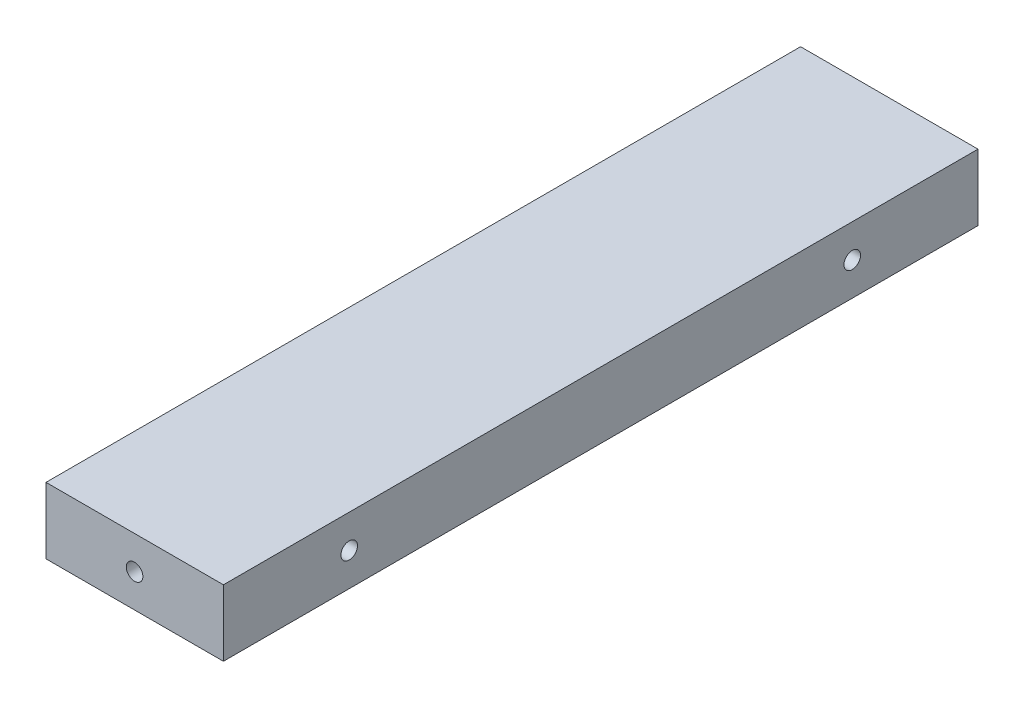
SolidWorks part; units mm, degrees
material "Beech"
ref_plane "Front Plane" through (0, 0, 0) normal (0, 0, 1) x (1, 0, 0)
ref_plane "Top Plane" through (0, 0, 0) normal (0, 1, 0) x (1, 0, 0)
ref_plane "Right Plane" through (0, 0, 0) normal (1, 0, 0) x (0, 0, -1)
sketch "Sketch1" plane through (0, 0, 0) normal (0, 0, 1) x (1, 0, 0)
  line L0 (-6.0809, -132.7) -> (-6.0809, 132.7) construction
  line L1 (-40.0809, -120) -> (-6.0809, -120)
  line L2 (-40.0809, -120) -> (-40.0809, -132.7)
  line L3 (-40.0809, -132.7) -> (-6.0809, -132.7)
  line L4 (-6.0809, -120) -> (-6.0809, -132.7)
  dimension "D1" = 12.7
extrude "Boss-Extrude1" add sketch "Sketch1" along normal up to surface (144.6 mm away)
hole_wizard "Hole1" positions "Sketch2" profile "Sketch3" legacy
sketch "Sketch2" plane through (12.9191, 0, 155.0243) normal (1, 0, 0) x (0, -1, 0)
  line L21 (0, 109.0243) -> (0, 155.0243) construction
  point P37 (126.35, 161.3743)
  point P42 (146.0833, 4.0743)
  point P44 (172.1667, 4.0743)
  point P63 (126.35, 34.5243)
  point P65 (126.35, 130.9243)
  point P76 (-172.1667, 4.0743)
  point P77 (-146.0833, 4.0743)
  point P78 (-126.35, 34.5243)
  point P79 (-126.35, 130.9243)
  point P80 (-126.35, 161.3743)
sketch "Sketch3" plane through (12.9191, -126.35, -6.35) normal (0, 1, 0) x (0, 0, -1)
  line L0 (0, 0) -> (0, 32.7039)
  line L1 (0, 32.7039) -> (1.5875, 31.75)
  line L2 (1.5875, 31.75) -> (1.5875, 4.0177)
  line L3 (1.5875, 4.0177) -> (5.08, 0)
  line L4 (5.08, 0) -> (0, 0)
  line L5 (0, -14.3089) -> (0, 102.4216) construction
  line L6 (0, 32.7039) -> (-1.5875, 31.75) construction
  line L7 (-1.5875, 4.0177) -> (-5.08, 0) construction
  dimension "Diameter" = 3.175
  dimension "Depth" = 31.75
  dimension "C-Sink Diameter" = 10.16
  dimension "C-Sink Angle" = 82
  dimension "Drill Angle" = 118
hole_wizard "Hole2" positions "Sketch4" profile "Sketch5" legacy
sketch "Sketch4" plane through (12.9191, 0, -10.4243) normal (1, 0, 0) x (0, 1, 0)
  line L21 (0, 109.0243) -> (0, 155.0243) construction
  point P37 (126.35, 161.3743)
  point P42 (146.0833, 4.0743)
  point P44 (172.1667, 4.0743)
  point P63 (126.35, 34.5243)
  point P65 (126.35, 130.9243)
  point P76 (-172.1667, 4.0743)
  point P77 (-146.0833, 4.0743)
  point P78 (-126.35, 34.5243)
  point P79 (-126.35, 130.9243)
  point P80 (-126.35, 161.3743)
sketch "Sketch5" plane through (12.9191, 126.35, 150.95) normal (0, 1, 0) x (0, 0, -1)
  line L0 (0, 0) -> (0, 32.7039)
  line L1 (0, 32.7039) -> (1.5875, 31.75)
  line L2 (1.5875, 31.75) -> (1.5875, 4.0177)
  line L3 (1.5875, 4.0177) -> (5.08, 0)
  line L4 (5.08, 0) -> (0, 0)
  line L5 (0, -14.3089) -> (0, 102.4216) construction
  line L6 (0, 32.7039) -> (-1.5875, 31.75) construction
  line L7 (-1.5875, 4.0177) -> (-5.08, 0) construction
  dimension "Diameter" = 3.175
  dimension "Depth" = 31.75
  dimension "C-Sink Diameter" = 10.16
  dimension "C-Sink Angle" = 82
  dimension "Drill Angle" = 118
hole_wizard "Hole5" positions "Sketch8" profile "Sketch9" legacy
sketch "Sketch8" plane through (-195.3677, 0, 157.3) normal (0, 0, 1) x (0, -1, 0)
  line L0 (120, 172.2617) -> (217.3, 172.2617) construction
  point P8 (126.35, 172.2617)
  point P10 (207.775, 172.2617)
sketch "Sketch9" plane through (-23.1059, -207.775, 157.3) normal (1, 0, 0) x (0, -1, 0)
  line L0 (0, 0) -> (0, 32.7039)
  line L1 (0, 32.7039) -> (1.5875, 31.75)
  line L2 (1.5875, 31.75) -> (1.5875, 4.0177)
  line L3 (1.5875, 4.0177) -> (5.08, 0)
  line L4 (5.08, 0) -> (0, 0)
  line L5 (0, -14.3089) -> (0, 102.4216) construction
  line L6 (0, 32.7039) -> (-1.5875, 31.75) construction
  line L7 (-1.5875, 4.0177) -> (-5.08, 0) construction
  dimension "Diameter" = 3.175
  dimension "Depth" = 31.75
  dimension "C-Sink Diameter" = 10.16
  dimension "C-Sink Angle" = 82
  dimension "Drill Angle" = 118
hole_wizard "Hole6" positions "Sketch10" profile "Sketch11" legacy
sketch "Sketch10" plane through (-52.7809, 0, -10.4243) normal (-1, 0, 0) x (0, -1, 0)
  line L12 (0, 0) -> (0, 155.0243) construction
  point P0 (-207.775, 333.0214)
  point P3 (-207.775, 225.489)
  point P6 (-207.775, 137.4243)
  point P9 (-172.1667, 4.0743)
  point P12 (-146.0833, 4.0743)
  point P15 (-94.6, 161.3743)
  point P18 (0, 161.3743)
  point P21 (94.6, 161.3743)
  point P24 (146.0833, 4.0743)
  point P27 (172.1667, 4.0743)
  point P30 (207.775, 137.4243)
  point P33 (207.775, 225.489)
  point P36 (207.775, 333.0214)
  point P39 (166.7958, 301.9704)
  point P42 (40.9792, 301.9704)
  point P45 (-40.9792, 301.9704)
  point P48 (-166.7958, 301.9704)
  point P51 (0, 193.1243)
  point P54 (0, 301.9704)
  point P57 (0, 412.3664)
  point P80 (-126.35, 106.8243)
  point P82 (-126.35, 58.6243)
  point P96 (126.35, 58.6243)
  point P97 (126.35, 106.8243)
sketch "Sketch11" plane through (-52.7809, 207.775, 322.5971) normal (0, 1, 0) x (0, 0, 1)
  line L0 (0, 0) -> (0, 32.7039)
  line L1 (0, 32.7039) -> (1.5875, 31.75)
  line L2 (1.5875, 31.75) -> (1.5875, 4.0177)
  line L3 (1.5875, 4.0177) -> (5.08, 0)
  line L4 (5.08, 0) -> (0, 0)
  line L5 (0, -14.3089) -> (0, 102.4216) construction
  line L6 (0, 32.7039) -> (-1.5875, 31.75) construction
  line L7 (-1.5875, 4.0177) -> (-5.08, 0) construction
  dimension "Diameter" = 3.175
  dimension "Depth" = 31.75
  dimension "C-Sink Diameter" = 10.16
  dimension "C-Sink Angle" = 82
  dimension "Drill Angle" = 118
hole_wizard "Hole7" positions "Sketch12" profile "Sketch13" legacy
sketch "Sketch12" plane through (-52.7809, 0, 155.0243) normal (-1, 0, 0) x (0, 1, 0)
  line L12 (0, 0) -> (0, 155.0243) construction
  point P0 (-207.775, 333.0214)
  point P3 (-207.775, 225.489)
  point P6 (-207.775, 137.4243)
  point P9 (-172.1667, 4.0743)
  point P12 (-146.0833, 4.0743)
  point P15 (-94.6, 161.3743)
  point P18 (0, 161.3743)
  point P21 (94.6, 161.3743)
  point P24 (146.0833, 4.0743)
  point P27 (172.1667, 4.0743)
  point P30 (207.775, 137.4243)
  point P33 (207.775, 225.489)
  point P36 (207.775, 333.0214)
  point P39 (166.7958, 301.9704)
  point P42 (40.9792, 301.9704)
  point P45 (-40.9792, 301.9704)
  point P48 (-166.7958, 301.9704)
  point P51 (0, 193.1243)
  point P54 (0, 301.9704)
  point P57 (0, 412.3664)
  point P80 (-126.35, 106.8243)
  point P82 (-126.35, 58.6243)
  point P96 (126.35, 58.6243)
  point P97 (126.35, 106.8243)
sketch "Sketch13" plane through (-52.7809, -207.775, -177.9971) normal (0, 1, 0) x (0, 0, 1)
  line L0 (0, 0) -> (0, 32.7039)
  line L1 (0, 32.7039) -> (1.5875, 31.75)
  line L2 (1.5875, 31.75) -> (1.5875, 4.0177)
  line L3 (1.5875, 4.0177) -> (5.08, 0)
  line L4 (5.08, 0) -> (0, 0)
  line L5 (0, -14.3089) -> (0, 102.4216) construction
  line L6 (0, 32.7039) -> (-1.5875, 31.75) construction
  line L7 (-1.5875, 4.0177) -> (-5.08, 0) construction
  dimension "Diameter" = 3.175
  dimension "Depth" = 31.75
  dimension "C-Sink Diameter" = 10.16
  dimension "C-Sink Angle" = 82
  dimension "Drill Angle" = 118
